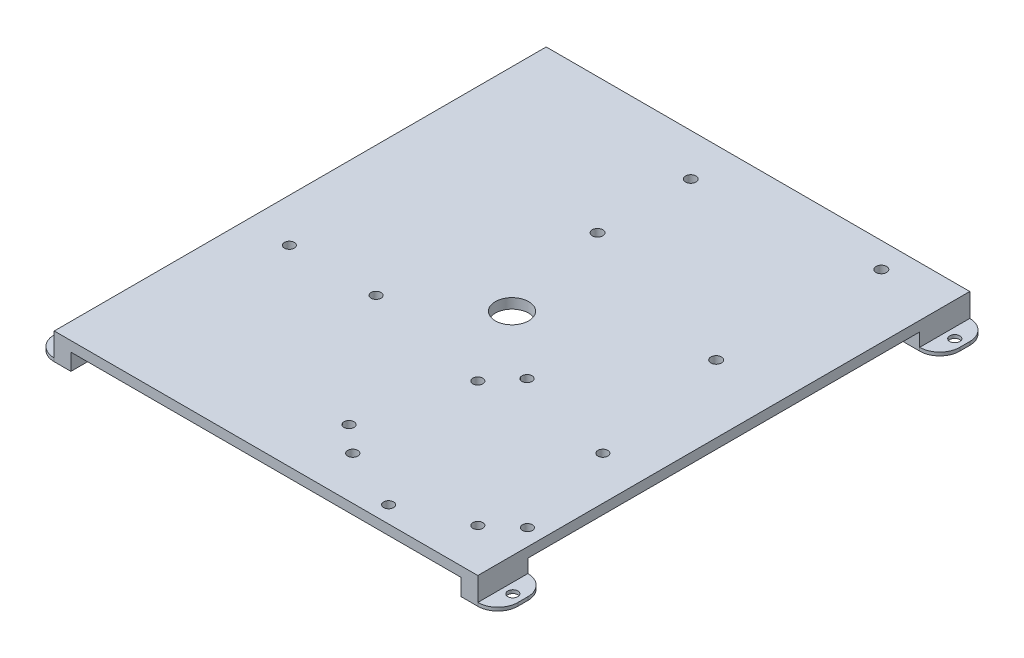
SolidWorks part; units mm, degrees
ref_plane "Front Plane" through (0, 0, 0) normal (0, 0, 1) x (1, 0, 0)
ref_plane "Top Plane" through (0, 0, 0) normal (0, 1, 0) x (1, 0, 0)
ref_plane "Right Plane" through (0, 0, 0) normal (1, 0, 0) x (0, 0, -1)
sketch "Base Sketch" plane through (0, 0, 0) normal (0, 1, 0) x (1, 0, 0)
  line L0 (0, 73.75) -> (0, -73.75) construction
  line L1 (-63.5, 73.75) -> (63.5, 73.75)
  line L2 (-63.5, 73.75) -> (-63.5, -73.75)
  line L3 (-63.5, -73.75) -> (63.5, -73.75)
  line L4 (63.5, 73.75) -> (63.5, -73.75)
  line L5 (-63.5, 73.75) -> (63.5, -73.75) construction
  line L6 (-63.5, -73.75) -> (63.5, 73.75) construction
  circle A0 centre (0, 0) radius 5
  point P0 (0, 0)
  dimension "D3" = 10
  dimension "D1" = 127
  dimension "D2" = 147.5
extrude "Base" add sketch "Base Sketch" along normal blind 3
sketch "Legs Sketch" plane through (0, 0, 0) normal (0, -1, 0) x (1, 0, 0)
  line L0 (0, 73.75) -> (0, -73.75) construction
  line L1 (-63.5, -73.75) -> (-58.5, -73.75)
  line L2 (-63.5, -73.75) -> (-63.5, -58.75)
  line L3 (-63.5, -58.75) -> (-58.5, -58.75)
  line L4 (-58.5, -73.75) -> (-58.5, -58.75)
  line L5 (-63.5, 73.75) -> (63.5, 73.75) construction
  line L6 (63.5, -73.75) -> (-63.5, -73.75) construction
  line L7 (63.5, -73.75) -> (58.5, -73.75)
  line L8 (63.5, -73.75) -> (63.5, -58.75)
  line L9 (63.5, -58.75) -> (58.5, -58.75)
  line L10 (58.5, -73.75) -> (58.5, -58.75)
  line L11 (63.5, 0) -> (-63.5, 0) construction
  line L12 (63.5, 73.75) -> (63.5, -73.75) construction
  line L13 (-63.5, -73.75) -> (-63.5, 73.75) construction
  line L14 (-63.5, 73.75) -> (-58.5, 73.75)
  line L15 (-63.5, 73.75) -> (-63.5, 58.75)
  line L16 (-63.5, 58.75) -> (-58.5, 58.75)
  line L17 (-58.5, 73.75) -> (-58.5, 58.75)
  line L18 (63.5, 73.75) -> (58.5, 73.75)
  line L19 (63.5, 73.75) -> (63.5, 58.75)
  line L20 (58.5, 73.75) -> (58.5, 58.75)
  line L21 (63.5, 58.75) -> (58.5, 58.75)
  dimension "D1" = 15
  dimension "D2" = 5
extrude "Legs" add sketch "Legs Sketch" along normal blind 5
sketch "Mount Sketch" plane through (63.5, 0, 0) normal (1, 0, 0) x (0, 0, -1)
  line L0 (-58.75, -5) -> (-58.75, 0) construction
  line L1 (-73.75, -5) -> (-58.75, -5)
  line L2 (-73.75, -5) -> (-73.75, -4)
  line L3 (-73.75, -4) -> (-58.75, -4)
  line L4 (-58.75, -5) -> (-58.75, -4)
  line L5 (0, 3) -> (0, 0) construction
  line L6 (-73.75, 3) -> (73.75, 3) construction
  line L7 (-58.75, 0) -> (58.75, 0) construction
  line L8 (58.75, -5) -> (58.75, -4)
  line L9 (73.75, -5) -> (58.75, -5)
  line L10 (73.75, -4) -> (58.75, -4)
  line L11 (73.75, -5) -> (73.75, -4)
  dimension "D1" = 1
extrude "Mount" add sketch "Mount Sketch" along normal blind 6
fillet "Dont cut urself" radius 6 4 edges at (69.5, -4.5, 58.75) (69.5, -4.5, 73.75) (69.5, -4.5, -73.75) (69.5, -4.5, -58.75)
sketch "Mounting Hole Sketch" plane through (0, -4, 0) normal (0, 1, 0) x (1, 0, 0)
  line L0 (69.5, -66.25) -> (63.5, -66.25) construction
  line L3 (69.5, -64.75) -> (69.5, -67.75) construction
  line L5 (63.5, -58.75) -> (63.5, -73.75) construction
  circle A1 centre (66.5, -66.25) radius 1.5
  dimension "D1" = 3
extrude "Mounting Hole 1" cut sketch "Mounting Hole Sketch" against normal through all
sketch "Mounting Hole 2 Sketch" plane through (0, -4, 0) normal (0, 1, 0) x (1, 0, 0)
  line L0 (63.5, 66.25) -> (69.5, 66.25) construction
  line L3 (63.5, 73.75) -> (63.5, 58.75) construction
  line L4 (69.5, 67.75) -> (69.5, 64.75) construction
  circle A1 centre (66.5, 66.25) radius 1.5
  dimension "D1" = 3
extrude "Mounting Hole 2" cut sketch "Mounting Hole 2 Sketch" against normal through all
sketch "Mount 2 Sketch" plane through (-63.5, 0, 0) normal (-1, 0, 0) x (0, 0, 1)
  line L0 (-58.75, -5) -> (-58.75, 0) construction
  line L1 (-73.75, -5) -> (-58.75, -5)
  line L2 (-73.75, -5) -> (-73.75, -4)
  line L3 (-73.75, -4) -> (-58.75, -4)
  line L4 (-58.75, -5) -> (-58.75, -4)
  line L5 (0, 3) -> (0, 0) construction
  line L6 (-73.75, 3) -> (73.75, 3) construction
  line L7 (-58.75, 0) -> (58.75, 0) construction
  line L8 (73.75, -4) -> (58.75, -4)
  line L9 (58.75, -5) -> (58.75, -4)
  line L10 (73.75, -5) -> (58.75, -5)
  line L11 (73.75, -5) -> (73.75, -4)
  dimension "D1" = 1
extrude "Mount 2" add sketch "Mount 2 Sketch" along normal blind 6
fillet "Dont cut urself 2" radius 6 4 edges at (-69.5, -4.5, 73.75) (-69.5, -4.5, 58.75) (-69.5, -4.5, -58.75) (-69.5, -4.5, -73.75)
sketch "Mounting Hole 3 Sketch" plane through (0, -4, 0) normal (0, 1, 0) x (1, 0, 0)
  line L0 (-69.5, -66.25) -> (-63.5, -66.25) construction
  line L1 (-69.5, -67.75) -> (-69.5, -64.75) construction
  line L2 (-63.5, -73.75) -> (-63.5, -58.75) construction
  circle A0 centre (-66.5, -66.25) radius 1.5
  dimension "D1" = 3
extrude "Mounting Hole 3" cut sketch "Mounting Hole 3 Sketch" against normal through all
sketch "Mounting Hole 4 Sketch" plane through (0, -4, 0) normal (0, 1, 0) x (1, 0, 0)
  line L0 (-69.5, 66.25) -> (-63.5, 66.25) construction
  line L1 (-69.5, 64.75) -> (-69.5, 67.75) construction
  line L2 (-63.5, 58.75) -> (-63.5, 73.75) construction
  circle A0 centre (-66.5, 66.25) radius 1.5
  dimension "D1" = 3
extrude "Mounting Hole 4" cut sketch "Mounting Hole 4 Sketch" against normal through all
sketch "Holes for Parts Sketch" plane through (0, 3, 0) normal (0, 1, 0) x (1, 0, 0)
  line L0 (-63.5, -73.75) -> (63.5, -73.75) construction
  line L1 (61.5, -71.75) -> (2, -71.75) construction
  line L2 (61.5, -71.75) -> (61.5, -12.25) construction
  line L3 (61.5, -12.25) -> (2, -12.25) construction
  line L4 (2, -71.75) -> (2, -12.25) construction
  line L5 (63.5, -73.75) -> (63.5, 73.75) construction
  line L6 (55.5, -65.75) -> (55.5, -18.25) construction
  line L7 (55.5, -18.25) -> (8, -18.25) construction
  line L8 (8, -65.75) -> (8, -18.25) construction
  line L9 (55.5, -65.75) -> (8, -65.75) construction
  line L10 (63.5, 73.75) -> (-63.5, 73.75) construction
  line L11 (58.5, 15.41) -> (-10.08, 15.41) construction
  line L12 (58.5, 15.41) -> (58.5, 68.75)
  line L13 (58.5, 68.75) -> (-10.08, 68.75) construction
  line L14 (-10.08, 15.41) -> (-10.08, 68.75) construction
  line L15 (-7.54, 15.41) -> (-7.54, 68.75) construction
  line L16 (-63.5, 73.75) -> (-63.5, -73.75) construction
  line L17 (-21.5, -48.75) -> (-53.5, -48.75) construction
  line L18 (-21.5, -48.75) -> (-21.5, 16.25) construction
  line L19 (-21.5, 16.25) -> (-53.5, 16.25) construction
  line L20 (-53.5, -48.75) -> (-53.5, 16.25) construction
  line L21 (-28.5, -48.75) -> (-28.5, -23.75)
  line L22 (-46.5, -48.75) -> (-46.5, -23.75) construction
  line L23 (58.5, 15.41) -> (-7.54, 15.41)
  line L24 (58.5, 68.75) -> (-7.54, 68.75)
  line L25 (-10.08, 63.67) -> (-10.08, 30.9)
  line L26 (-7.54, 15.41) -> (-7.54, 28.36)
  line L27 (-7.54, 68.75) -> (-7.54, 66.21)
  line L28 (-7.54, 66.21) -> (-10.08, 63.67)
  line L29 (-7.54, 28.36) -> (-10.08, 30.9)
  line L30 (-28.5, -48.75) -> (-46.5, -48.75)
  line L31 (-28.5, 16.25) -> (-46.5, 16.25)
  line L32 (-28.5, -8.75) -> (-21.5, -8.75)
  line L33 (-21.5, -8.75) -> (-21.5, -23.75)
  line L34 (-21.5, -23.75) -> (-28.5, -23.75)
  line L35 (-28.5, -8.75) -> (-28.5, 16.25)
  line L36 (-46.5, -8.75) -> (-53.5, -8.75)
  line L37 (-53.5, -8.75) -> (-53.5, -23.75)
  line L38 (-53.5, -23.75) -> (-46.5, -23.75)
  line L39 (-46.5, 16.25) -> (-46.5, -8.75)
  line L40 (-46.5, -23.75) -> (-46.5, -48.75)
  line L41 (-46.5, -8.75) -> (-46.5, 16.25) construction
  line L42 (-46.5, -8.75) -> (-46.5, -23.75) construction
  line L43 (-28.5, -8.75) -> (-28.5, -23.75) construction
  line L44 (31.75, -65.75) -> (31.75, -71.75) construction
  line L45 (39.25, -71.75) -> (24.25, -71.75)
  line L46 (55.5, -65.75) -> (39.25, -65.75)
  line L47 (39.25, -65.75) -> (39.25, -71.75)
  line L48 (24.25, -65.75) -> (24.25, -71.75)
  line L49 (24.25, -65.75) -> (8, -65.75)
  line L50 (55.5, -42) -> (61.5, -42) construction
  line L51 (55.5, -65.75) -> (55.5, -61.375)
  line L52 (55.5, -42) -> (55.5, -46.375)
  line L53 (55.5, -18.25) -> (55.5, -42)
  line L54 (55.5, -46.375) -> (61.5, -46.375)
  line L55 (61.5, -46.375) -> (61.5, -61.375)
  line L56 (61.5, -61.375) -> (55.5, -61.375)
  line L57 (8, -46.375) -> (2, -46.375)
  line L58 (2, -46.375) -> (2, -61.375)
  line L59 (2, -61.375) -> (8, -61.375)
  line L60 (8, -65.75) -> (8, -61.375)
  line L61 (8, -46.375) -> (8, -18.25)
  line L62 (55.5, -18.25) -> (31.5, -18.25)
  line L64 (27.25, -12.25) -> (27.25, -18.25)
  line L65 (27.25, -18.25) -> (31.5, -18.25)
  line L66 (27.25, -12.25) -> (12.25, -12.25)
  line L67 (12.25, -12.25) -> (12.25, -18.25)
  line L68 (12.25, -18.25) -> (8, -18.25)
  line L69 (61.5, -53.875) -> (55.5, -53.875) construction
  line L70 (2, -53.875) -> (8, -53.875) construction
  line L71 (19.75, -12.25) -> (19.75, -18.25) construction
  line L72 (-47.5, -23.75) -> (-47.5, -8.75) construction
  line L73 (-53.5, -16.25) -> (-47.5, -16.25) construction
  line L74 (-27.5, -23.75) -> (-27.5, -8.75) construction
  line L75 (-21.5, -16.25) -> (-27.5, -16.25) construction
  line L77 (53.5, -63.75) -> (10, -63.75)
  line L78 (53.5, -63.75) -> (53.5, -20.25)
  line L79 (53.5, -20.25) -> (10, -20.25)
  line L80 (10, -63.75) -> (10, -20.25)
  circle A0 centre (31.75, -68.75) radius 1.5
  circle A1 centre (58.5, -53.875) radius 1.5
  circle A2 centre (5, -53.875) radius 1.5
  circle A3 centre (19.75, -15.25) radius 1.5
  circle A4 centre (-50.5, -16.25) radius 1.5
  circle A5 centre (-24.5, -16.25) radius 1.5
  circle A6 centre (-7.54, 33.19) radius 1.59
  circle A7 centre (-7.54, 61.13) radius 1.59
  circle A8 centre (44.53, 66.21) radius 1.59
  circle A9 centre (43.26, 17.95) radius 1.59
  circle A10 centre (50.5, -60.75) radius 1.5
  circle A11 centre (13, -60.75) radius 1.5
  circle A12 centre (13, -23.25) radius 1.5
  circle A13 centre (50.5, -23.25) radius 1.5
  point P101 (16.125, -65.75)
  dimension "D30" = 3
  dimension "D34" = 3.18
  dimension "D1" = 2
  dimension "D2" = 2
  dimension "D3" = 59.5
  dimension "D4" = 59.5
  dimension "D6" = 5
  dimension "D7" = 5
  dimension "D8" = 68.58
  dimension "D9" = 53.34
  dimension "D10" = 2.54
  dimension "D11" = 10
  dimension "D12" = 24
  dimension "D13" = 65
  dimension "D14" = 7
  dimension "D15" = 18
  dimension "D16" = 25
  dimension "D17" = 5.08
  dimension "D18" = 2.54
  dimension "D19" = 12.95
  dimension "D20" = 32.77
  dimension "D21" = 15
  dimension "D22" = 25
  dimension "D23" = 25
  dimension "D24" = 7.5
  dimension "D25" = 7.5
  dimension "D26" = 4.375
  dimension "D27" = 4.375
  dimension "D28" = 15
  dimension "D29" = 4.25
  dimension "D31" = 1
  dimension "D32" = 1
  dimension "D33" = 17.78
  dimension "D35" = 7.62
  dimension "D36" = 2.54
  dimension "D37" = 13.97
  dimension "D38" = 2.54
  dimension "D39" = 15.24
  dimension "D40" = 2
  dimension "D41" = 2
  dimension "D42" = 2
  dimension "D43" = 2
  dimension "D44" = 3
  dimension "D45" = 3
  dimension "D48" = 3
  dimension "D49" = 3
  dimension "D50" = 3
  dimension "D5" = 6
  dimension "D46" = 2
  dimension "D47" = 2
sketch "Piece Placement" plane through (0, 3, 0) normal (0, 1, 0) x (1, 0, 0)
  line L0 (58.5, 15.41) -> (58.5, 68.75)
  line L1 (53.5, -63.75) -> (10, -63.75)
  line L2 (53.5, -63.75) -> (53.5, -20.25)
  line L3 (53.5, -20.25) -> (10, -20.25)
  line L4 (10, -63.75) -> (10, -20.25)
  line L5 (-28.5, -48.75) -> (-46.5, -48.75)
  line L6 (-28.5, -48.75) -> (-28.5, 16.25)
  line L7 (-28.5, 16.25) -> (-46.5, 16.25)
  line L8 (-46.5, -48.75) -> (-46.5, 16.25)
  line L9 (58.5, 68.75) -> (-7.54, 68.75)
  line L10 (-7.54, 68.75) -> (-7.54, 66.21)
  line L11 (-7.54, 66.21) -> (-10.08, 63.67)
  line L12 (-10.08, 63.67) -> (-10.08, 30.9)
  line L13 (-10.08, 30.9) -> (-7.54, 28.36)
  line L14 (-7.54, 28.36) -> (-7.54, 15.41)
  line L15 (58.5, 15.41) -> (-7.54, 15.41)
  line L17 (55.5, -65.75) -> (8, -65.75)
  line L18 (55.5, -65.75) -> (55.5, -18.25)
  line L19 (55.5, -18.25) -> (8, -18.25)
  line L20 (8, -65.75) -> (8, -18.25)
  line L25 (60.5, 13.41) -> (-9.54, 13.41)
  line L26 (-9.54, 27.5316) -> (-9.54, 13.41)
  line L27 (-12.08, 30.0716) -> (-9.54, 27.5316)
  line L28 (-12.08, 64.4984) -> (-12.08, 30.0716)
  line L29 (-9.54, 67.0384) -> (-12.08, 64.4984)
  line L30 (-9.54, 70.75) -> (-9.54, 67.0384)
  line L31 (60.5, 70.75) -> (-9.54, 70.75)
  line L32 (60.5, 13.41) -> (60.5, 70.75)
  dimension "D1" = 2
extrude "Holes for Parts" cut sketch "Holes for Parts Sketch" against normal up to next contours A10 | A1 | A13 | A12 | A3 | A2 | A11 | A0 | A5 | A4 | A6 | A7 | A8 | A9
